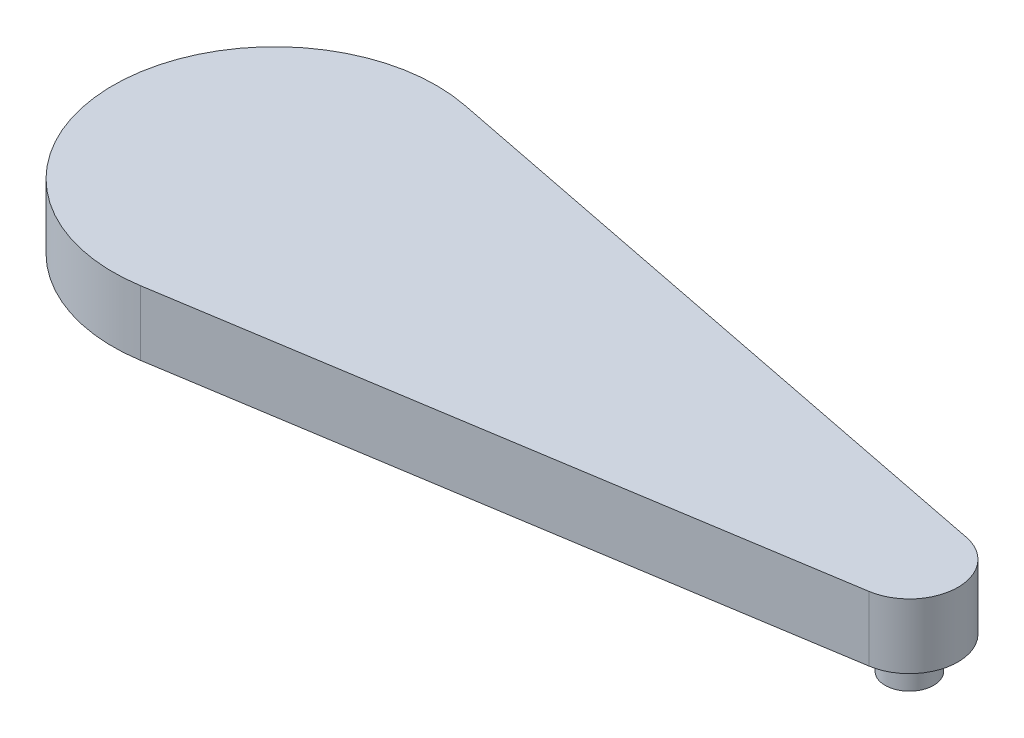
SolidWorks part; units mm, degrees
ref_plane "Front Plane" through (0, 0, 0) normal (0, 0, 1) x (1, 0, 0)
ref_plane "Top Plane" through (0, 0, 0) normal (0, 1, 0) x (1, 0, 0)
ref_plane "Right Plane" through (0, 0, 0) normal (1, 0, 0) x (0, 0, -1)
sketch "Sketch1" plane through (0, 0, 0) normal (0, 1, 0) x (1, 0, 0)
  line L0 (101.452, 5.4616) -> (4.8402, 24.527)
  line L1 (0, 0) -> (100, -1.8965) construction
  line L2 (101.172, -9.3044) -> (3.9067, -24.6929)
  arc A0 (4.8402, 24.527) -> (3.9067, -24.6929) centre (0, 0) ccw
  arc A1 (101.172, -9.3044) -> (101.452, 5.4616) centre (100, -1.8965) ccw
  dimension "D1" = 50
  dimension "D2" = 15
  dimension "D3" = 100
extrude "Boss-Extrude1" add sketch "Sketch1" along normal blind 10
sketch "Sketch3" plane through (0, 0, 0) normal (0, -1, 0) x (1, 0, 0)
  line L0 (17.5294, -2.9529) -> (1.076, -5.9027)
  line L1 (17.5294, 2.9529) -> (1.076, 5.9027)
  line L2 (-17.5294, -2.9529) -> (-1.076, -5.9027)
  line L3 (-17.5294, 2.9529) -> (-1.076, 5.9027)
  line L4 (-17, 0) -> (17, 0) construction
  arc A0 (17.5294, -2.9529) -> (17.5294, 2.9529) centre (17, 0) ccw
  arc A1 (-17.5294, 2.9529) -> (-17.5294, -2.9529) centre (-17, 0) ccw
  arc A2 (1.076, 5.9027) -> (-1.076, 5.9027) centre (0, 0) ccw
  arc A3 (-1.076, -5.9027) -> (1.076, -5.9027) centre (0, 0) ccw
  circle A4 centre (100, 1.8965) radius 3.75
  dimension "D2" = 3
  dimension "D3" = 3
  dimension "D5" = 6
  dimension "D9" = 6
  dimension "D15" = 7.5
  dimension "D1" = 34
  dimension "D4" = 16.7158
  dimension "D6" = 16.7158
  dimension "D7" = 16.7158
  dimension "D8" = 16.7158
  dimension "D10" = 6
  dimension "D11" = 6
  dimension "D12" = 6
  dimension "D13" = 6
extrude "Cut-Extrude1" cut sketch "Sketch3" against normal blind 5
sketch "Sketch4" plane through (0, 5, 0) normal (0, -1, 0) x (1, 0, 0)
  circle A0 centre (100, 1.8965) radius 3.75
extrude "Boss-Extrude2" add sketch "Sketch4" along normal blind 10
